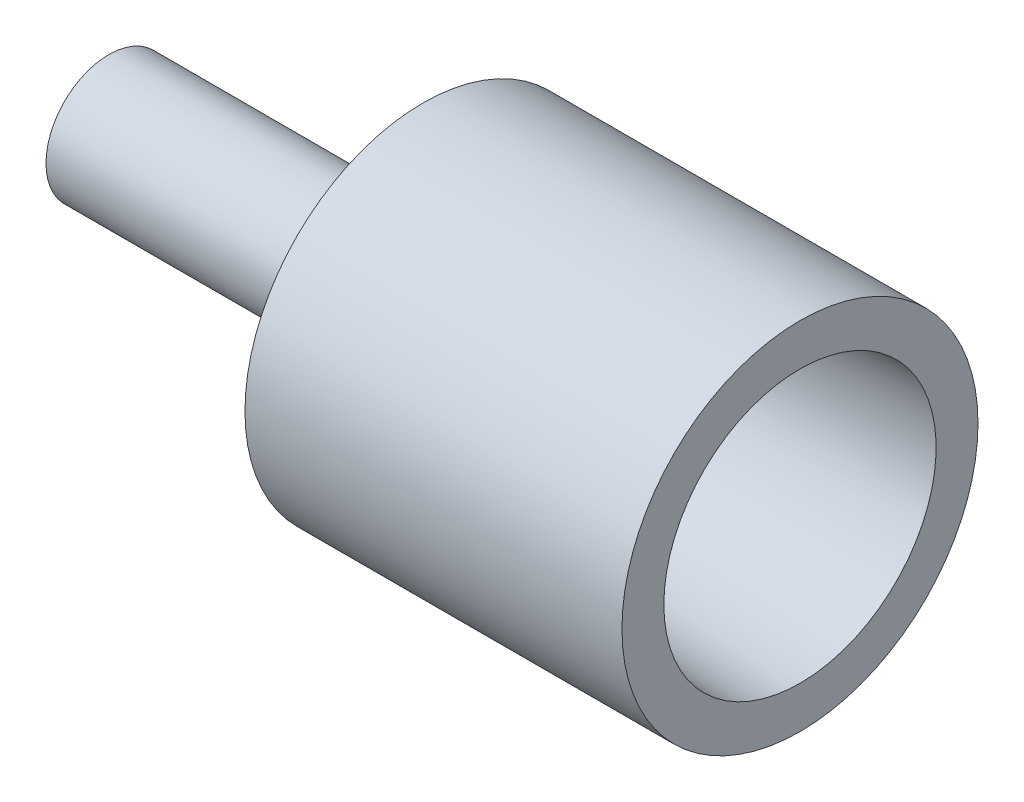
SolidWorks part; units mm, degrees
ref_plane "前视基准面" through (0, 0, 0) normal (0, 0, 1) x (1, 0, 0)
ref_plane "上视基准面" through (0, 0, 0) normal (0, 1, 0) x (1, 0, 0)
ref_plane "右视基准面" through (0, 0, 0) normal (1, 0, 0) x (0, 0, -1)
sketch "草图1" plane through (0, 0, 0) normal (0, 1, 0) x (1, 0, 0)
  line L0 (15, 8.5) -> (-3, 8.5)
  line L1 (-3, 8.5) -> (-3, 3)
  line L2 (-3, 3) -> (-18, 3)
  line L3 (-18, 3) -> (-18, 0)
  line L4 (-18, 0) -> (0, 0)
  line L5 (0, 0) -> (0, 5.75)
  line L6 (0, 5.75) -> (15, 6.5)
  line L7 (15, 6.5) -> (15, 8.5)
  point P3 (0, 0)
  dimension "D1" = 5.75
  dimension "D2" = 6.5
  dimension "D3" = 15
  dimension "D4" = 2
  dimension "D5" = 3
  dimension "D6" = 3
  dimension "D7" = 15
revolve "旋转1" add sketch "草图1" angle 360 about L4
chamfer "倒角1" distance 3 angle 45 1 edges at (-3, 0, 3)
